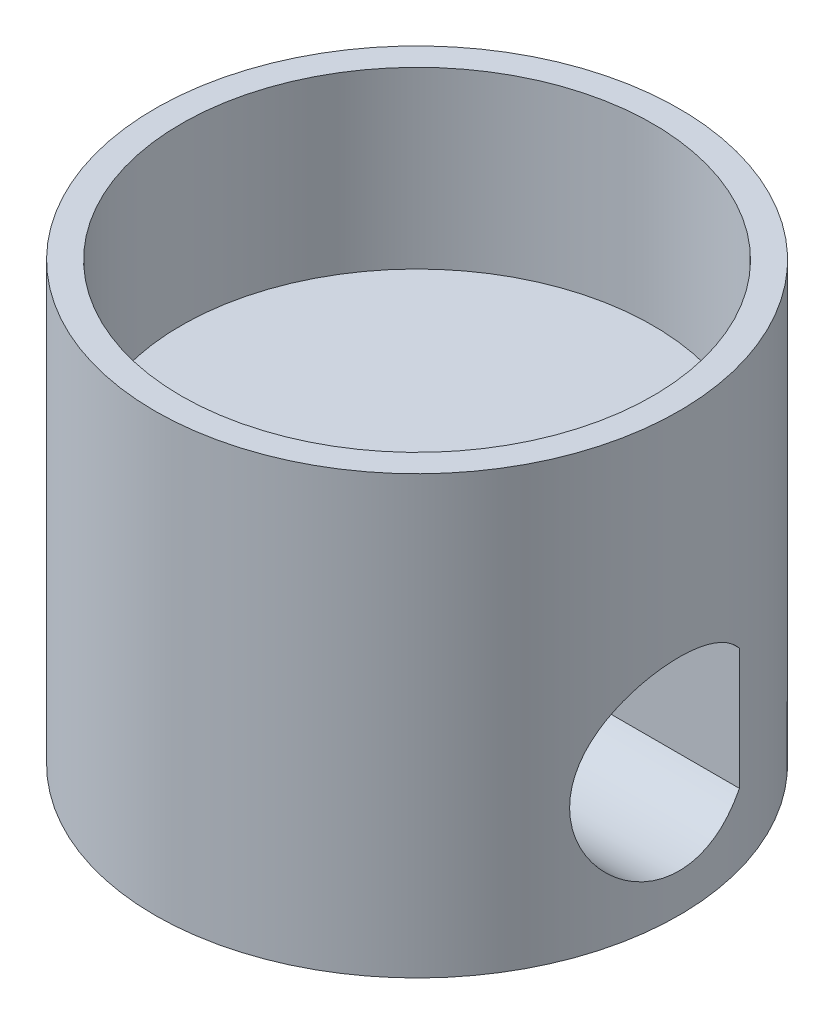
SolidWorks part; units mm, degrees
material "ABS"
ref_plane "Plano frontal" through (0, 0, 0) normal (0, 0, 1) x (1, 0, 0)
ref_plane "Plano superior" through (0, 0, 0) normal (0, 1, 0) x (1, 0, 0)
ref_plane "Plano direito" through (0, 0, 0) normal (1, 0, 0) x (0, 0, -1)
sketch "Esboço1" plane through (0, 0, 0) normal (0, 1, 0) x (1, 0, 0)
  circle A0 centre (0, 0) radius 15
  dimension "D1" = 30
extrude "Ressalto-extrusão1" add sketch "Esboço1" along normal blind 25
sketch "Esboço2" plane through (0, 25, 0) normal (0, 1, 0) x (1, 0, 0)
  circle A0 centre (0, 0) radius 13.5
  dimension "D1" = 27
extrude "Corte-extrusão1" cut sketch "Esboço2" against normal blind 10
sketch "Esboço4" plane through (0, 0, 0) normal (1, 0, 0) x (0, 0, -1)
  line L0 (-19.1578, 20) -> (19.404, 20) construction
  line L1 (15, 25) -> (-15, 25) construction
  line L2 (-19.0041, 7.5) -> (19.407, 7.5) construction
  line L3 (-15, 0) -> (15, 0) construction
  line L4 (0, -1.7776) -> (0, 21.9601) construction
  line L6 (6.6, 2.5) -> (4, 2.5)
  line L7 (6.6, 2.5) -> (6.6, 12.5)
  line L8 (6.6, 12.5) -> (4, 12.5)
  line L9 (4, 2.5) -> (4, 12.5)
  line L10 (6.6, 2.5) -> (4, 12.5) construction
  line L11 (6.6, 12.5) -> (4, 2.5) construction
  circle A0 centre (0, 7.5) radius 5.3
  point P15 (5.3, 7.5)
  dimension "D3" = 10.6
  dimension "D1" = 5
  dimension "D2" = 7.5
  dimension "D4" = 10
  dimension "D5" = 2.6
extrude "Corte-extrusão3" cut sketch "Esboço4" against normal through all both and the other way through all contours L9 A0
